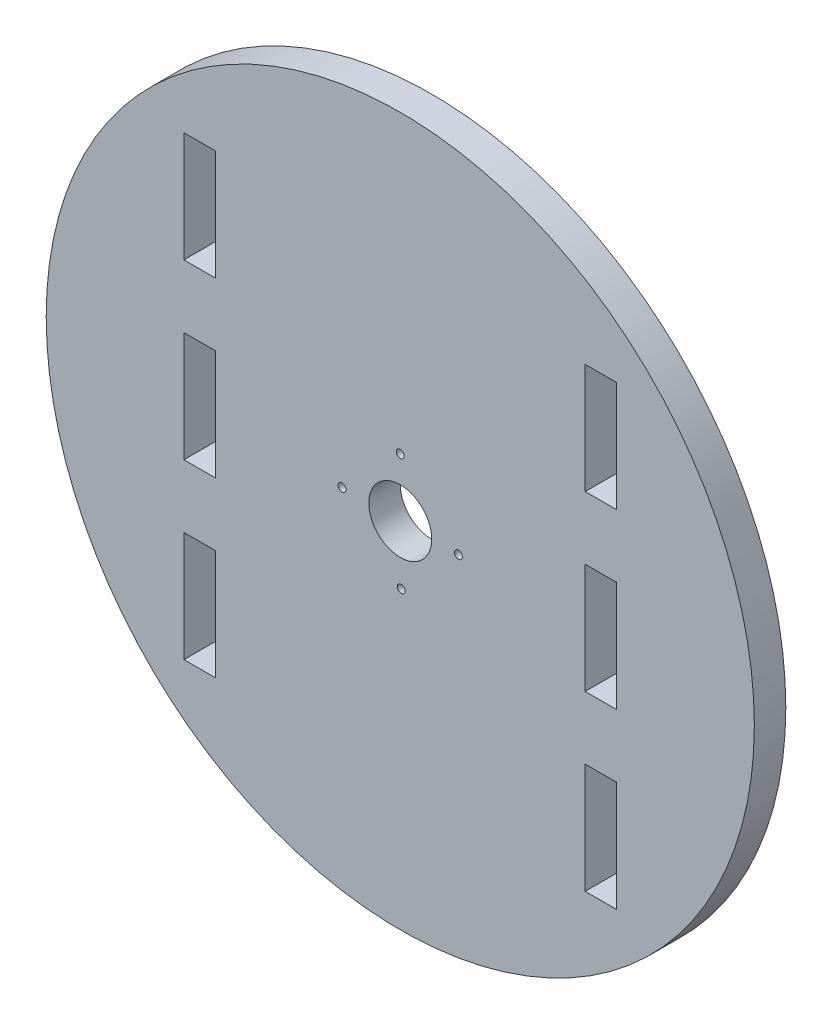
SolidWorks part; units mm, degrees
material "Beech"
ref_plane "Front Plane" through (0, 0, 0) normal (0, 0, 1) x (1, 0, 0)
ref_plane "Top Plane" through (0, 0, 0) normal (0, 1, 0) x (1, 0, 0)
ref_plane "Right Plane" through (0, 0, 0) normal (1, 0, 0) x (0, 0, -1)
sketch "Sketch1" plane through (0, 0, 0) normal (0, 0, 1) x (1, 0, 0)
  line L0 (68.5, 74) -> (72.5, 74)
  line L1 (72.5, 16) -> (68.5, 16)
  line L2 (68.5, 60) -> (72.5, 60)
  line L3 (68.5, 30) -> (72.5, 30)
  line L4 (68.5, 52) -> (72.5, 52)
  line L5 (72.5, 52) -> (72.5, 38)
  line L6 (72.5, 38) -> (68.5, 38)
  line L7 (72.5, 74) -> (72.5, 60)
  line L8 (68.5, 30) -> (68.5, 16)
  line L9 (72.5, 30) -> (72.5, 16)
  line L10 (68.5, 38) -> (68.5, 52)
  line L11 (17.5, 60) -> (21.5, 60)
  line L12 (17.5, 30) -> (21.5, 30)
  line L13 (17.5, 52) -> (21.5, 52)
  line L14 (21.5, 52) -> (21.5, 38)
  line L15 (21.5, 38) -> (17.5, 38)
  line L16 (17.5, 60) -> (17.5, 74)
  line L17 (21.5, 74) -> (21.5, 60)
  line L18 (17.5, 30) -> (17.5, 16)
  line L19 (21.5, 30) -> (21.5, 16)
  line L20 (17.5, 38) -> (17.5, 52)
  line L21 (17.5, 74) -> (21.5, 74)
  line L22 (17.5, 16) -> (21.5, 16)
  line L23 (17.5, 72.75) -> (17.5, 65.25)
  line L24 (68.5, 74) -> (68.5, 60)
  circle A0 centre (45, 45) radius 45
  circle A1 centre (45, 45) radius 4
  circle A2 centre (45, 52.4) radius 0.5
  circle A3 centre (45.121, 37.601) radius 0.5
  circle A4 centre (52.4, 45) radius 0.5
  circle A5 centre (37.6, 45) radius 0.5
extrude "Boss-Extrude1" add sketch "Sketch1" along normal blind 4 contours A0 A5 A4 A3 A2 A1 L16 L21 L17 L11 L6 L10 L4 L5 L3 L9 L1 L8 L15 L20 L13 L14 L22 L18 L12 L19 L24 L0 L7 L2
